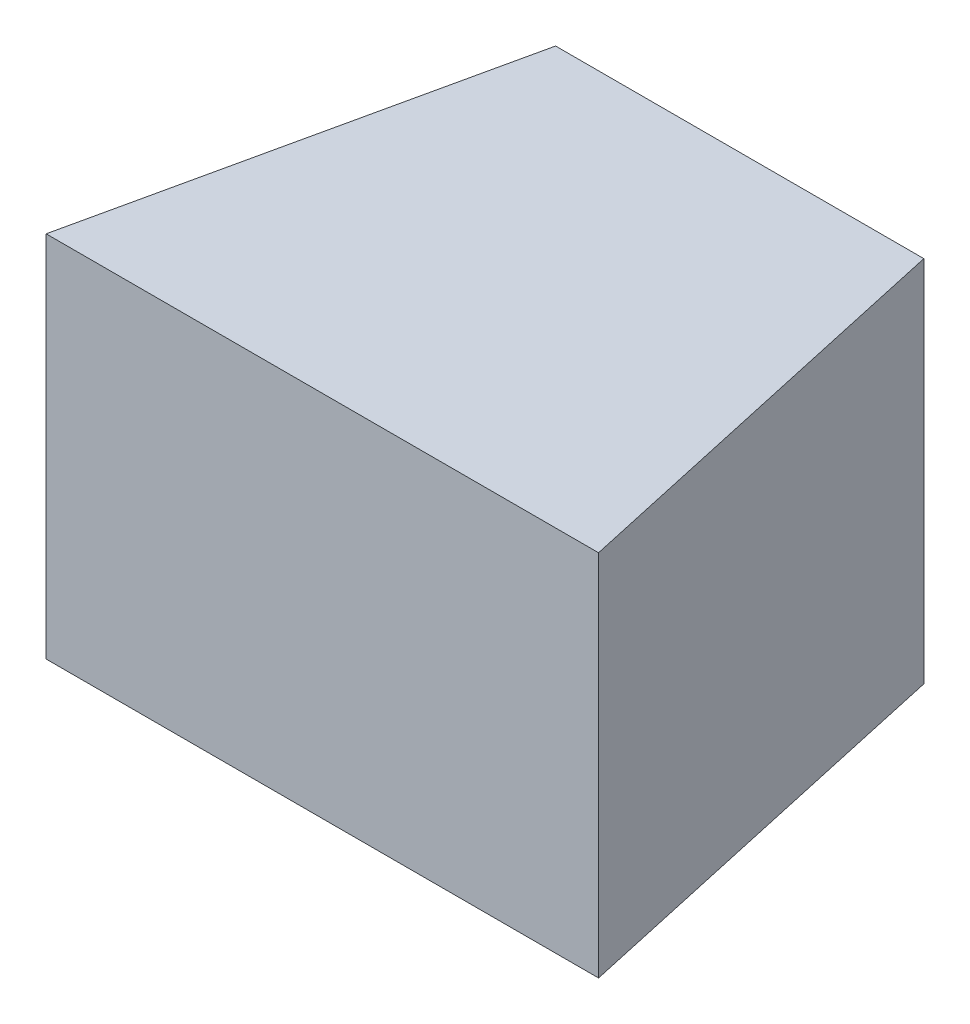
SolidWorks part; units mm, degrees
material "鎳"
ref_plane "前基準面" through (0, 0, 0) normal (0, 0, 1) x (1, 0, 0)
ref_plane "上基準面" through (0, 0, 0) normal (0, 1, 0) x (1, 0, 0)
ref_plane "右基準面" through (0, 0, 0) normal (1, 0, 0) x (0, 0, -1)
sketch "草圖1" plane through (0, 0, 0) normal (0, 1, 0) x (1, 0, 0)
  line L0 (-22.5, -17) -> (-15, 17)
  line L1 (-22.5, 17) -> (22.5, 17)
  line L2 (-22.5, 17) -> (-22.5, -17)
  line L3 (-22.5, -17) -> (22.5, -17)
  line L4 (22.5, 17) -> (22.5, -17)
  line L5 (-22.5, 17) -> (22.5, -17) construction
  line L6 (-22.5, -17) -> (22.5, 17) construction
  line L7 (22.5, -17) -> (15, 17)
  point P0 (0, 0)
  dimension "D1" = 45
  dimension "D2" = 34
  dimension "D3" = 30
extrude "填料-伸長1" add sketch "草圖1" along normal blind 30 contours L3 L7 L1 L0
sketch3d "URDF Reference"
  line L0 (0, 0, 0) -> (10, 0, 0) construction
  line L1 (0, 0, 0) -> (0, 0, -10) construction
  point P0 (0, 0, 0)
  point P1 (0, 0, 0)
